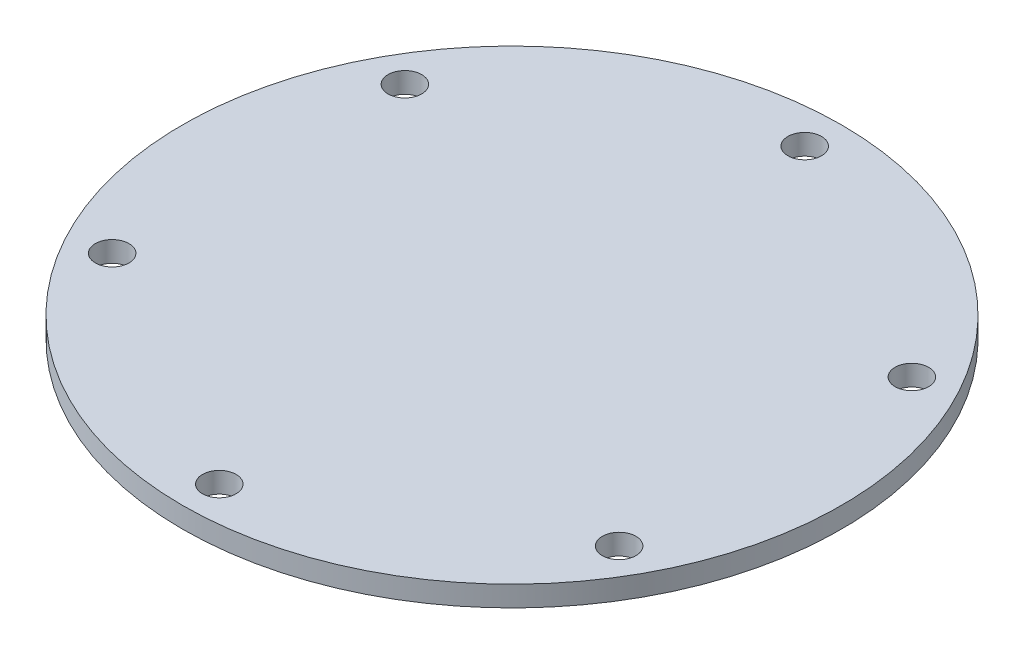
SolidWorks part; units mm, degrees
material "ABS"
ref_plane "Front Plane" through (0, 0, 0) normal (0, 0, 1) x (1, 0, 0)
ref_plane "Top Plane" through (0, 0, 0) normal (0, 1, 0) x (1, 0, 0)
ref_plane "Right Plane" through (0, 0, 0) normal (1, 0, 0) x (0, 0, -1)
sketch "Sketch1" plane through (0, 0, 0) normal (0, 1, 0) x (1, 0, 0)
  circle A1 centre (0, 0) radius 50.8
  circle A2 centre (0, 0) radius 50.8 construction
extrude "Boss-Extrude1" add sketch "Sketch1" along normal blind 3.175
hole_wizard "#6 (0.204) Diameter Hole1" positions "Sketch7" profile "Sketch6" hole size "#6" standard "ANSI Inch" end condition through all
sketch "Sketch7" plane through (0, 3.175, 0) normal (0, 1, 0) x (1, 0, 0)
  circle A1 centre (0, 0) radius 45.1199 construction
  circle A3 centre (0, 45.1199) radius 2.5908 construction
  circle A4 centre (0, 45.1199) radius 2.5908
  point P0 (0, 45.1199)
  dimension "D2" = 90.2398
sketch "Sketch6" plane through (0, 3.175, -45.1199) normal (1, 0, 0) x (0, 0, 1)
  line L0 (0, 0) -> (0, 3.175)
  line L1 (0, 3.175) -> (2.5908, 3.175)
  line L2 (2.5908, 3.175) -> (2.5908, 0)
  line L5 (2.5908, 0) -> (0, 0)
  line L11 (0, -6.35) -> (0, 107.95) construction
  dimension "Thru Hole Dia." = 5.1816
  dimension "Thru Hole Depth" = 3.175
pattern_circular "CirPattern1" count 6 over 360 about axis through (0, 0, 0) along (0, 1, 0) of "#6 (0.204) Diameter Hole1"
